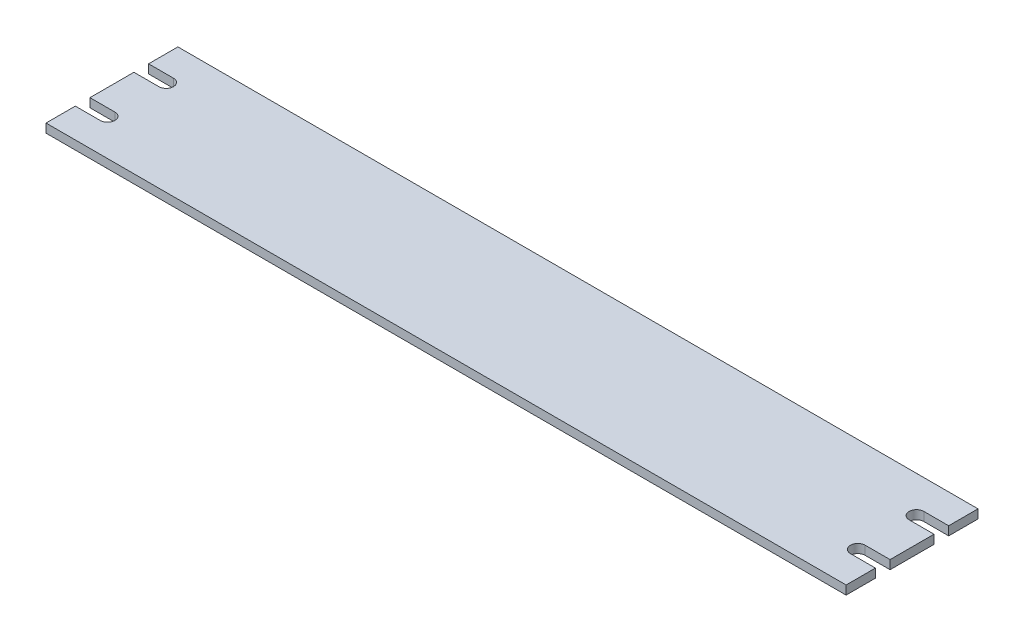
SolidWorks part; units mm, degrees
material "6061-T6 (SS)"
ref_plane "Front Plane" through (0, 0, 0) normal (0, 0, 1) x (1, 0, 0)
ref_plane "Top Plane" through (0, 0, 0) normal (0, 1, 0) x (1, 0, 0)
ref_plane "Right Plane" through (0, 0, 0) normal (1, 0, 0) x (0, 0, -1)
sketch "Sketch2" plane through (0, 0, 0) normal (0, 1, 0) x (1, 0, 0)
  line L1 (136.5, -22.5) -> (-136.5, -22.5)
  line L2 (136.5, -22.5) -> (136.5, 22.5)
  line L3 (136.5, 22.5) -> (-136.5, 22.5)
  line L4 (-136.5, -22.5) -> (-136.5, 22.5)
  line L5 (136.5, -22.5) -> (-136.5, 22.5) construction
  line L6 (136.5, 22.5) -> (-136.5, -22.5) construction
  point P0 (0, 0)
  dimension "D1" = 45
  dimension "D2" = 273
extrude "Boss-Extrude1" add sketch "Sketch2" along normal blind 3
sketch "Sketch3" plane through (0, 3, 0) normal (0, 1, 0) x (1, 0, 0)
  line L0 (-136.5, 10) -> (-128, 10) construction
  line L1 (-136.5, 22.5) -> (-136.5, -22.5) construction
  line L2 (-136.5, 12.5) -> (-128, 12.5)
  line L3 (-136.5, 7.5) -> (-128, 7.5)
  line L4 (-136.5, 0) -> (-271.296, 0) construction
  line L5 (-136.5, -10) -> (-128, -10) construction
  line L6 (-136.5, -12.5) -> (-128, -12.5)
  line L7 (-136.5, -7.5) -> (-128, -7.5)
  line L8 (0, 0) -> (0, 42.4581) construction
  line L9 (136.5, 10) -> (128, 10) construction
  line L10 (136.5, 12.5) -> (128, 12.5)
  line L11 (136.5, 7.5) -> (128, 7.5)
  line L12 (136.5, -10) -> (128, -10) construction
  line L13 (136.5, -12.5) -> (128, -12.5)
  line L14 (136.5, -7.5) -> (128, -7.5)
  arc A0 (-136.5, 12.5) -> (-136.5, 7.5) centre (-136.5, 10) ccw
  arc A1 (-128, 7.5) -> (-128, 12.5) centre (-128, 10) ccw
  arc A2 (-136.5, -12.5) -> (-136.5, -7.5) centre (-136.5, -10) cw
  arc A3 (-128, -7.5) -> (-128, -12.5) centre (-128, -10) cw
  arc A4 (136.5, 12.5) -> (136.5, 7.5) centre (136.5, 10) cw
  arc A5 (128, 7.5) -> (128, 12.5) centre (128, 10) cw
  arc A6 (136.5, -12.5) -> (136.5, -7.5) centre (136.5, -10) ccw
  arc A7 (128, -7.5) -> (128, -12.5) centre (128, -10) ccw
  point P4 (-132.25, 10)
  point P14 (-132.25, -10)
  point P23 (132.25, 10)
  point P30 (132.25, -10)
  dimension "D1" = 5
  dimension "D2" = 8.5
  dimension "D3" = 20
extrude "Cut-Extrude1" cut sketch "Sketch3" against normal through all
